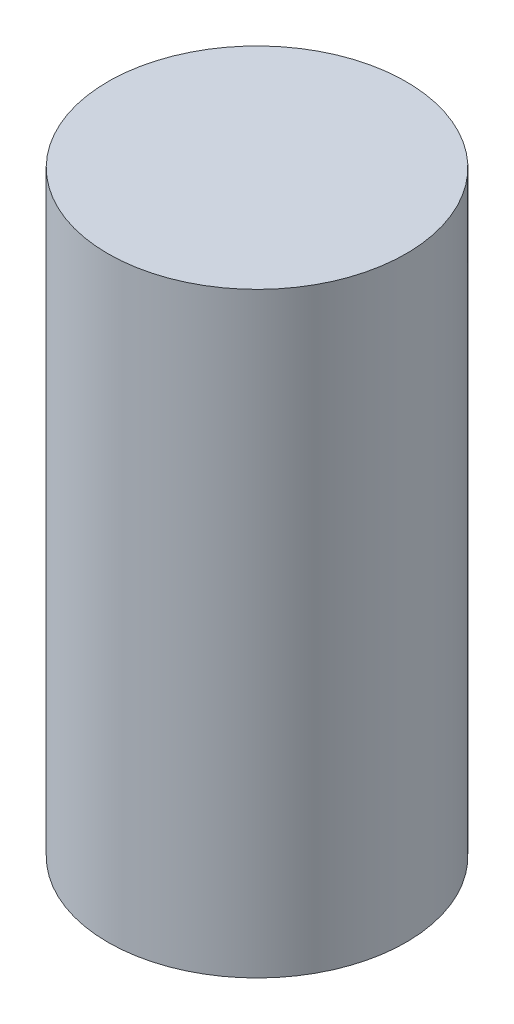
SolidWorks part; units mm, degrees
ref_plane "Front Plane" through (0, 0, 0) normal (0, 0, 1) x (1, 0, 0)
ref_plane "Top Plane" through (0, 0, 0) normal (0, 1, 0) x (1, 0, 0)
ref_plane "Right Plane" through (0, 0, 0) normal (1, 0, 0) x (0, 0, -1)
sketch "Sketch2" plane through (0, 0, 0) normal (0, 1, 0) x (1, 0, 0)
  circle A0 centre (0, 0) radius 20
  dimension "D1" = 40
extrude "Boss-Extrude1" add sketch "Sketch2" along normal blind 80
